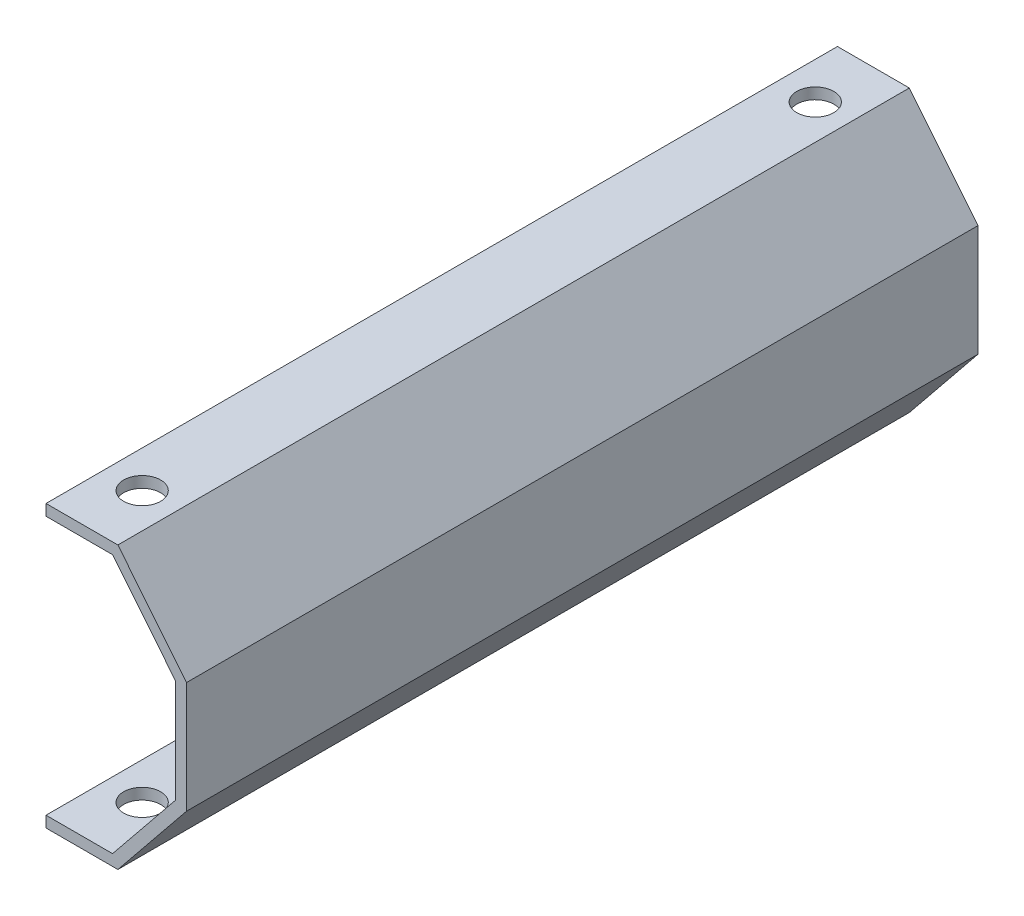
SolidWorks part; units mm, degrees
ref_plane "Alzado" through (0, 0, 0) normal (0, 0, 1) x (1, 0, 0)
ref_plane "Planta" through (0, 0, 0) normal (0, 1, 0) x (1, 0, 0)
ref_plane "Vista lateral" through (0, 0, 0) normal (1, 0, 0) x (0, 0, -1)
sketch "Croquis1" plane through (0, 0, 0) normal (0, 0, 1) x (1, 0, 0)
  line L0 (0, 0) -> (9, 0)
  line L1 (17.5, 17.5) -> (-30.8706, 17.5) construction
  line L2 (17.5, 10.5) -> (17.5, 24.5)
  line L3 (9, 0) -> (17.5, 10.5)
  line L4 (0, 35) -> (9, 35)
  line L5 (9, 35) -> (17.5, 24.5)
  line L6 (0, -1.5) -> (9.7156, -1.5)
  line L7 (9.7156, -1.5) -> (19, 9.969)
  line L8 (19, 9.969) -> (19, 25.031)
  line L9 (9.7156, 36.5) -> (19, 25.031)
  line L10 (0, 36.5) -> (9.7156, 36.5)
  line L11 (0, 0) -> (0, -1.5)
  line L12 (0, 36.5) -> (0, 35)
  dimension "D1" = 9
  dimension "D2" = 14
  dimension "D3" = 35
  dimension "D5" = 19
  dimension "D4" = 1.5
extrude "Saliente-Extruir1" add sketch "Croquis1" along normal blind 107
sketch "Croquis3" plane through (0, 36.5, 0) normal (0, 1, 0) x (1, 0, 0)
  line L0 (9.7156, 0) -> (0, 0) construction
  line L1 (9, -107) -> (9, 0) construction
  line L2 (9.7156, -53.5) -> (0, -53.5) construction
  line L3 (9.7156, -107) -> (9.7156, 0) construction
  line L4 (0, -107) -> (0, 0) construction
  circle A0 centre (5, -8) radius 2.5
  circle A1 centre (5, -99) radius 2.5
  dimension "D1" = 5
  dimension "D2" = 8
  dimension "D3" = 4
extrude "Cortar-Extruir1" cut sketch "Croquis3" against normal up to next
sketch "Croquis4" plane through (0, -1.5, 0) normal (0, -1, 0) x (1, 0, 0)
  line L0 (0, 0) -> (9.7156, 0) construction
  line L1 (9, 107) -> (9, 0) construction
  line L2 (9.7156, 53.5) -> (0, 53.5) construction
  line L3 (9.7156, 107) -> (9.7156, 0) construction
  line L4 (0, 107) -> (0, 0) construction
  circle A0 centre (5, 8) radius 2.5
  circle A1 centre (5, 99) radius 2.5
  dimension "D1" = 5
  dimension "D2" = 8
  dimension "D3" = 4
extrude "Cortar-Extruir2" cut sketch "Croquis4" against normal up to next
